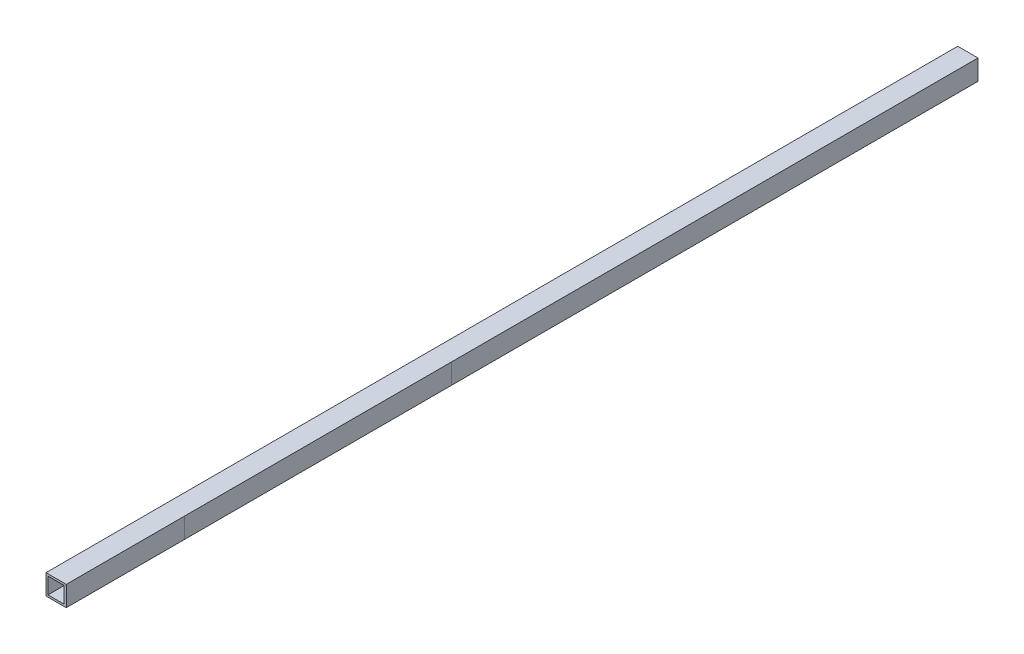
SolidWorks part; units mm, degrees
material "Alaşım Çelik"
ref_plane "Ön Düzlem" through (0, 0, 0) normal (0, 0, 1) x (1, 0, 0)
ref_plane "Üst Düzlem" through (0, 0, 0) normal (0, 1, 0) x (1, 0, 0)
ref_plane "Sağ Düzlem" through (0, 0, 0) normal (1, 0, 0) x (0, 0, -1)
sketch "Çizim1" plane through (0, 0, 0) normal (0, 0, 1) x (1, 0, 0)
  line L1 (0, 0) -> (40, 0)
  line L2 (0, 0) -> (0, 40)
  line L3 (0, 40) -> (40, 40)
  line L4 (40, 0) -> (40, 40)
  line L5 (4, 4) -> (36, 4)
  line L6 (4, 4) -> (4, 36)
  line L7 (4, 36) -> (36, 36)
  line L8 (36, 4) -> (36, 36)
  dimension "D1" = 40
  dimension "D2" = 40
  dimension "D3" = 4
  dimension "D4" = 4
  dimension "D5" = 4
  dimension "D6" = 4
extrude "Yükseklik-Ekstrüzyon1" add sketch "Çizim1" against normal blind 1800
sketch "Çizim2" plane through (40, 0, 0) normal (1, 0, 0) x (0, 0, -1)
  line L0 (760.8872, 116.3032) -> (760.8872, -70.6383)
  line L1 (233.4305, 116.3032) -> (233.4305, -54.5696)
split line "Ayrım Çizgisi1"
